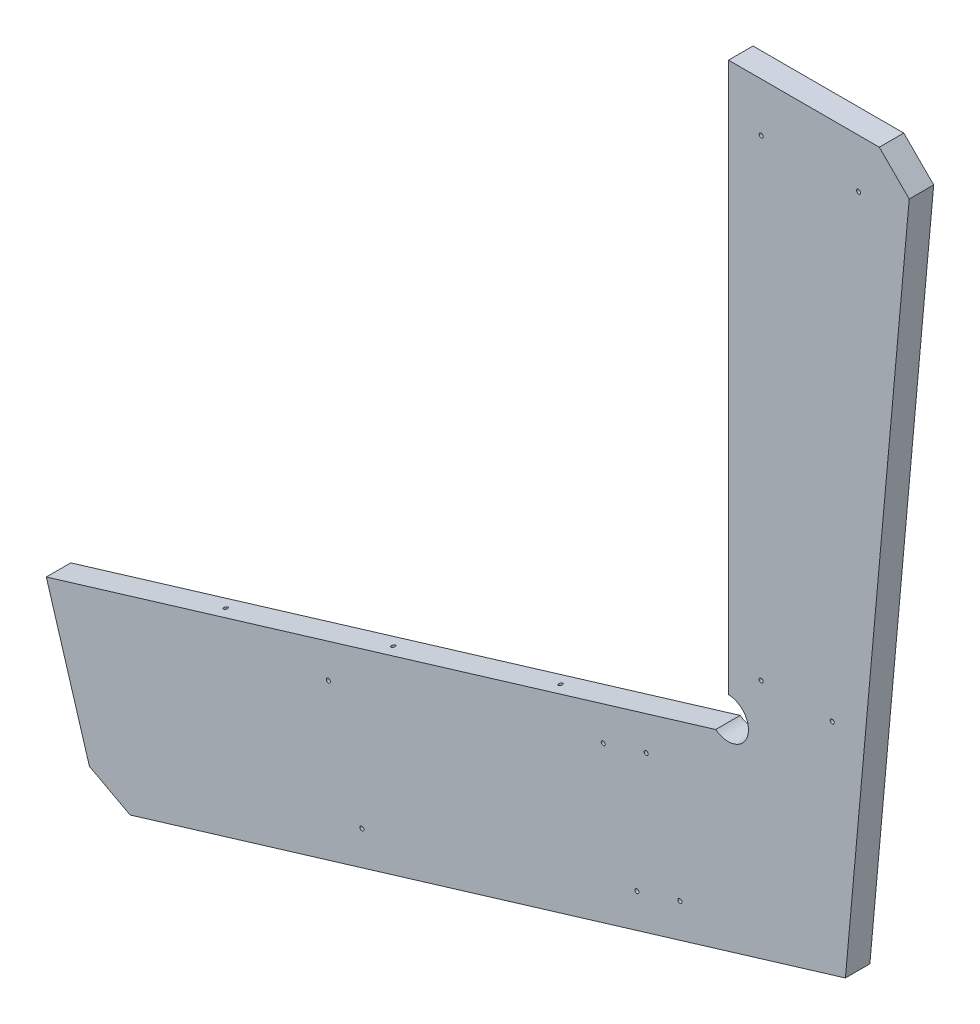
SolidWorks part; units mm, degrees
material "Beech"
ref_plane "Front Plane" through (0, 0, 0) normal (0, 0, 1) x (1, 0, 0)
ref_plane "Top Plane" through (0, 0, 0) normal (0, 1, 0) x (1, 0, 0)
ref_plane "Right Plane" through (0, 0, 0) normal (1, 0, 0) x (0, 0, -1)
sketch "Sketch1" plane through (0, 0, 0) normal (0, 0, 1) x (1, 0, 0)
  line L0 (12.7, 12.7) -> (12.7, -415.1856)
  line L1 (12.7, 12.7) -> (155.4923, 12.7)
  line L2 (155.4923, 12.7) -> (103.7007, -560.6863)
  line L3 (-525.0991, -623.2821) -> (-544.935, -557.7423) construction
  line L6 (2.6872, -443.6415) -> (-518.462, -601.37)
  line L7 (10.4775, 0) -> (-10.4775, 0) construction
  line L8 (-518.462, -601.37) -> (-477.5339, -736.6)
  line L9 (-522.1409, -589.2145) -> (-518.462, -601.37) construction
  line L10 (-518.462, -601.37) -> (16.3789, -439.4976) construction
  line L11 (-477.5339, -736.6) -> (103.7007, -560.6863)
  arc A0 (2.6872, -443.6415) -> (12.7, -415.1856) centre (12.3644, -431.057) ccw
  dimension "D3" = 31.75
  dimension "D1" = 736.6
  dimension "D2" = 112
  dimension "D4" = 129.6293
  dimension "D5" = 91.3362
extrude "Boss-Extrude1" add sketch "Sketch1" against normal blind 19.05
ref_plane "CL" through (0, 0, -9.525) normal (0, 0, 1) x (1, 0, 0)
chamfer "Chamfer1" distance 25.4 angle 45 2 edges at (-477.5339, -736.6, -9.525) (155.4923, 12.7, -9.525)
hole_wizard "Hole1" positions "Sketch2" profile "Sketch3" legacy
sketch "Sketch2" plane through (0, 10.4243, -184.525) normal (-1, 0, 0) x (0, 0, -1)
  line L8 (155.95, -2.2757) -> (155.95, 437.7664) construction
  line L11 (175, -2.2757) -> (175, 437.7664) construction
  line L15 (155.95, -2.2757) -> (155.95, 107.7348)
  line L16 (155.95, 107.7348) -> (155.95, 217.7454)
  line L17 (155.95, 217.7454) -> (155.95, 327.7559)
  line L18 (155.95, 327.7559) -> (155.95, 437.7664)
  line L20 (175, -2.2757) -> (175, 85.7327)
  line L21 (175, 85.7327) -> (175, 173.7411)
  line L22 (175, 173.7411) -> (175, 261.7496)
  line L23 (175, 261.7496) -> (175, 349.758)
  line L24 (175, 349.758) -> (175, 437.7664)
  line L25 (0, 155.0243) -> (0, 437.7664) construction
  point P36 (155.95, 107.7348)
  point P40 (155.95, 327.7559)
  point P46 (175, 85.7327)
  point P52 (175, 349.758)
  point P77 (-175, 349.758)
  point P80 (-175, 85.7327)
  point P81 (-155.95, 327.7559)
  point P83 (-155.95, 107.7348)
sketch "Sketch3" plane through (0, -97.3105, -28.575) normal (0, 1, 0) x (0, 0, 1)
  line L0 (0, 0) -> (0, 32.7039)
  line L1 (0, 32.7039) -> (1.5875, 31.75)
  line L2 (1.5875, 31.75) -> (1.5875, 4.0177)
  line L3 (1.5875, 4.0177) -> (5.08, 0)
  line L4 (5.08, 0) -> (0, 0)
  line L5 (0, -14.3089) -> (0, 102.4216) construction
  line L6 (0, 32.7039) -> (-1.5875, 31.75) construction
  line L7 (-1.5875, 4.0177) -> (-5.08, 0) construction
  dimension "Diameter" = 3.175
  dimension "Depth" = 31.75
  dimension "C-Sink Diameter" = 10.16
  dimension "C-Sink Angle" = 82
  dimension "Drill Angle" = 118
hole_wizard "Hole2" positions "Sketch4" profile "Sketch5" legacy
sketch "Sketch4" plane through (0, 10.4243, 165.475) normal (-1, 0, 0) x (0, 0, -1)
  line L8 (155.95, -2.2757) -> (155.95, 437.7664) construction
  line L11 (175, -2.2757) -> (175, 437.7664) construction
  line L15 (155.95, -2.2757) -> (155.95, 107.7348)
  line L16 (155.95, 107.7348) -> (155.95, 217.7454)
  line L17 (155.95, 217.7454) -> (155.95, 327.7559)
  line L18 (155.95, 327.7559) -> (155.95, 437.7664)
  line L20 (175, -2.2757) -> (175, 85.7327)
  line L21 (175, 85.7327) -> (175, 173.7411)
  line L22 (175, 173.7411) -> (175, 261.7496)
  line L23 (175, 261.7496) -> (175, 349.758)
  line L24 (175, 349.758) -> (175, 437.7664)
  line L25 (0, 155.0243) -> (0, 437.7664) construction
  point P36 (155.95, 107.7348)
  point P40 (155.95, 327.7559)
  point P46 (175, 85.7327)
  point P52 (175, 349.758)
  point P77 (-175, 349.758)
  point P80 (-175, 85.7327)
  point P81 (-155.95, 327.7559)
  point P83 (-155.95, 107.7348)
sketch "Sketch5" plane through (0, -97.3105, 321.425) normal (0, 1, 0) x (0, 0, 1)
  line L0 (0, 0) -> (0, 32.7039)
  line L1 (0, 32.7039) -> (1.5875, 31.75)
  line L2 (1.5875, 31.75) -> (1.5875, 4.0177)
  line L3 (1.5875, 4.0177) -> (5.08, 0)
  line L4 (5.08, 0) -> (0, 0)
  line L5 (0, -14.3089) -> (0, 102.4216) construction
  line L6 (0, 32.7039) -> (-1.5875, 31.75) construction
  line L7 (-1.5875, 4.0177) -> (-5.08, 0) construction
  dimension "Diameter" = 3.175
  dimension "Depth" = 31.75
  dimension "C-Sink Diameter" = 10.16
  dimension "C-Sink Angle" = 82
  dimension "Drill Angle" = 118
hole_wizard "Hole3" positions "Sketch6" profile "Sketch7" legacy
sketch "Sketch6" plane through (264.6961, -351.0742, -184.525) normal (-0.2897, 0.9571, 0) x (0, 0, -1)
  point P49 (175, 685.961)
  point P51 (175, 549.8373)
  point P53 (175, 413.7135)
  point P67 (81.55, 779.6497)
  point P73 (81.55, 652.3446)
  point P79 (62.5, 662.9534)
  point P83 (62.5, 769.041)
  point P103 (-62.5, 769.041)
  point P105 (-62.5, 662.9534)
  point P106 (-81.55, 652.3446)
  point P109 (-81.55, 779.6497)
  point P110 (-175, 413.7135)
  point P111 (-175, 549.8373)
  point P112 (-175, 685.961)
  point P115 (-82.7375, 600.3846)
  point P117 (0, 600.3846)
  point P119 (82.7375, 600.3846)
  point P129 (0, 376.7378)
  point P131 (-82.7375, 376.7378)
  point P133 (82.7375, 376.7378)
sketch "Sketch7" plane through (-391.8536, -549.7824, -359.525) normal (0, 0, 1) x (-0.9571, -0.2897, 0)
  line L0 (0, 0) -> (0, 32.7039)
  line L1 (0, 32.7039) -> (1.5875, 31.75)
  line L2 (1.5875, 31.75) -> (1.5875, 4.0177)
  line L3 (1.5875, 4.0177) -> (5.08, 0)
  line L4 (5.08, 0) -> (0, 0)
  line L5 (0, -14.3089) -> (0, 102.4216) construction
  line L6 (0, 32.7039) -> (-1.5875, 31.75) construction
  line L7 (-1.5875, 4.0177) -> (-5.08, 0) construction
  dimension "Diameter" = 3.175
  dimension "Depth" = 31.75
  dimension "C-Sink Diameter" = 10.16
  dimension "C-Sink Angle" = 82
  dimension "Drill Angle" = 118
hole_wizard "Hole4" positions "Sketch8" profile "Sketch9" legacy
sketch "Sketch8" plane through (264.6961, -351.0742, 165.475) normal (-0.2897, 0.9571, 0) x (0, 0, -1)
  point P49 (175, 685.961)
  point P51 (175, 549.8373)
  point P53 (175, 413.7135)
  point P67 (81.55, 779.6497)
  point P73 (81.55, 652.3446)
  point P79 (62.5, 662.9534)
  point P83 (62.5, 769.041)
  point P103 (-62.5, 769.041)
  point P105 (-62.5, 662.9534)
  point P106 (-81.55, 652.3446)
  point P109 (-81.55, 779.6497)
  point P110 (-175, 413.7135)
  point P111 (-175, 549.8373)
  point P112 (-175, 685.961)
  point P115 (-82.7375, 600.3846)
  point P117 (0, 600.3846)
  point P119 (82.7375, 600.3846)
  point P129 (0, 376.7378)
  point P131 (-82.7375, 376.7378)
  point P133 (82.7375, 376.7378)
sketch "Sketch9" plane through (-391.8536, -549.7824, -9.525) normal (0, 0, 1) x (-0.9571, -0.2897, 0)
  line L0 (0, 0) -> (0, 32.7039)
  line L1 (0, 32.7039) -> (1.5875, 31.75)
  line L2 (1.5875, 31.75) -> (1.5875, 4.0177)
  line L3 (1.5875, 4.0177) -> (5.08, 0)
  line L4 (5.08, 0) -> (0, 0)
  line L5 (0, -14.3089) -> (0, 102.4216) construction
  line L6 (0, 32.7039) -> (-1.5875, 31.75) construction
  line L7 (-1.5875, 4.0177) -> (-5.08, 0) construction
  dimension "Diameter" = 3.175
  dimension "Depth" = 31.75
  dimension "C-Sink Diameter" = 10.16
  dimension "C-Sink Angle" = 82
  dimension "Drill Angle" = 118
hole_wizard "Hole5" positions "Sketch10" profile "Sketch11" legacy
sketch "Sketch10" plane through (155.2867, 10.4243, -19.05) normal (0, 0, -1) x (-0.09, -0.9959, 0)
  line L0 (48.5061, 138.7859) -> (35.9701, 0) construction
  line L5 (414.5728, 105.7206) -> (405.0235, 0) construction
  line L7 (490.0108, 170.6797) -> (621.0107, 117.7523) construction
  line L12 (503.094, 203.0616) -> (634.0938, 150.1342) construction
  line L16 (586.8736, 410.4234) -> (717.8734, 357.496) construction
  line L19 (597.4602, 127.2674) -> (610.5433, 159.6493) construction
  line L20 (610.5433, 159.6493) -> (694.3229, 367.011) construction
  line L22 (513.5613, 161.1647) -> (526.6445, 193.5466) construction
  line L23 (526.6445, 193.5466) -> (610.424, 400.9084) construction
  point P0 (46.2211, 113.4889)
  point P2 (39.3976, 37.9455)
  point P4 (412.2879, 80.4236)
  point P51 (407.3085, 25.297)
  point P56 (513.5613, 161.1647)
  point P58 (597.4602, 127.2674)
  point P61 (610.5433, 159.6493)
  point P63 (694.3229, 367.011)
  point P66 (526.6445, 193.5466)
  point P68 (610.424, 400.9084)
sketch "Sketch11" plane through (38.1, -25.4, -19.05) normal (1, 0, 0) x (0, 1, 0)
  line L0 (0, 0) -> (0, 39.0539)
  line L1 (0, 39.0539) -> (1.5875, 38.1)
  line L2 (1.5875, 38.1) -> (1.5875, 4.0177)
  line L3 (1.5875, 4.0177) -> (5.08, 0)
  line L4 (5.08, 0) -> (0, 0)
  line L5 (0, -14.3089) -> (0, 102.4216) construction
  line L6 (0, 39.0539) -> (-1.5875, 38.1) construction
  line L7 (-1.5875, 4.0177) -> (-5.08, 0) construction
  dimension "Diameter" = 3.175
  dimension "Depth" = 38.1
  dimension "C-Sink Diameter" = 10.16
  dimension "C-Sink Angle" = 82
  dimension "Drill Angle" = 118
hole_wizard "Hole6" positions "Sketch12" profile "Sketch13" legacy
sketch "Sketch12" plane through (-643.7058, -231.395, 165.475) normal (-0.9571, -0.2897, 0) x (0, 0, -1)
  line L0 (207.775, 377.6924) -> (207.775, 288.0915) construction
  line L4 (108.65, 377.6924) -> (108.65, 288.0915) construction
  line L8 (175, 506.2803) -> (175, 390.3924) construction
  line L12 (94.25, 390.3924) -> (94.25, 377.6924) construction
  line L17 (94.25, 384.0424) -> (217.3, 384.0424) construction
  line L19 (94.25, 384.0424) -> (135.2667, 384.0424)
  line L20 (135.2667, 384.0424) -> (176.2833, 384.0424)
  line L21 (176.2833, 384.0424) -> (217.3, 384.0424)
  line L22 (0, 288.0915) -> (0, 390.3924) construction
  point P39 (108.65, 332.8919)
  point P41 (207.775, 332.8919)
  point P43 (175, 448.3363)
  point P47 (135.2667, 384.0424)
  point P49 (176.2833, 384.0424)
  point P65 (-175, 448.3363)
  point P66 (-135.2667, 384.0424)
  point P67 (-176.2833, 384.0424)
  point P68 (-207.775, 332.8919)
  point P69 (-108.65, 332.8919)
sketch "Sketch13" plane through (-547.2741, -550.0138, 274.125) normal (0, 0, 1) x (0.2897, -0.9571, 0)
  line L0 (0, 0) -> (0, 39.0539)
  line L1 (0, 39.0539) -> (1.5875, 38.1)
  line L2 (1.5875, 38.1) -> (1.5875, 4.0177)
  line L3 (1.5875, 4.0177) -> (5.08, 0)
  line L4 (5.08, 0) -> (0, 0)
  line L5 (0, -14.3089) -> (0, 102.4216) construction
  line L6 (0, 39.0539) -> (-1.5875, 38.1) construction
  line L7 (-1.5875, 4.0177) -> (-5.08, 0) construction
  dimension "Diameter" = 3.175
  dimension "Depth" = 38.1
  dimension "C-Sink Diameter" = 10.16
  dimension "C-Sink Angle" = 82
  dimension "Drill Angle" = 118
